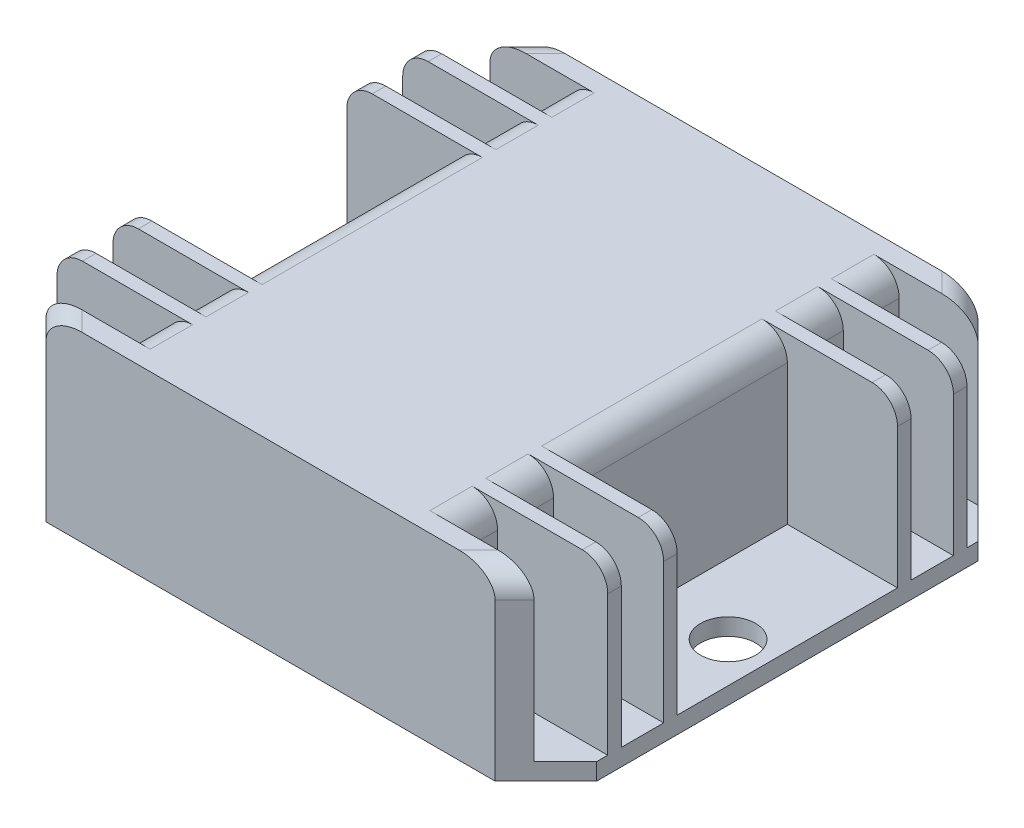
SolidWorks part; units mm, degrees
material "201.0-T43 Insulated Mold Casting (SS)"
ref_plane "Front Plane" through (0, 0, 0) normal (0, 0, 1) x (1, 0, 0)
ref_plane "Top Plane" through (0, 0, 0) normal (0, 1, 0) x (1, 0, 0)
ref_plane "Right Plane" through (0, 0, 0) normal (1, 0, 0) x (0, 0, -1)
sketch "Sketch1" plane through (0, 0, 0) normal (0, 1, 0) x (1, 0, 0)
  line L0 (0, -1000) -> (0, 49000) construction
  line L1 (-32.5, -28.5) -> (32.5, -28.5)
  line L2 (-32.5, -28.5) -> (-32.5, 28.5)
  line L3 (-32.5, 28.5) -> (32.5, 28.5)
  line L4 (32.5, -28.5) -> (32.5, 28.5)
  line L5 (-32.5, -28.5) -> (32.5, 28.5) construction
  line L6 (-32.5, 28.5) -> (32.5, -28.5) construction
  circle A0 centre (27.75, -2.25) radius 3.25
  circle A1 centre (-27.75, -2.25) radius 3.25
  point P0 (0, 0)
  dimension "D5" = 6.5
  dimension "D1" = 65
  dimension "D2" = 57
  dimension "D3" = 26.25
  dimension "D4" = 4.75
extrude "Boss-Extrude1" add sketch "Sketch1" along normal blind 21.5
chamfer "Chamfer1" distance 6 angle 45 4 edges at (32.5, 10.75, -28.5) (32.5, 10.75, 28.5) (-32.5, 10.75, -28.5) (-32.5, 10.75, 28.5)
sketch "Sketch2" plane through (0, 21.5, 0) normal (0, 1, 0) x (1, 0, 0)
  line L0 (-32.5, 22.5) -> (-32.5, -22.5) construction
  line L1 (-32.5, 13) -> (-19.5, 13)
  line L2 (-32.5, 13) -> (-32.5, -13)
  line L3 (-32.5, -13) -> (-19.5, -13)
  line L4 (-19.5, 13) -> (-19.5, -13)
  line L5 (0, -1000) -> (0, 49000) construction
  line L7 (-1000, 0) -> (49000, 0) construction
  line L8 (-32.5, 14.6) -> (-19.5, 14.6)
  line L9 (-32.5, 14.6) -> (-32.5, 19.6)
  line L10 (-32.5, 19.6) -> (-19.5, 19.6)
  line L11 (-19.5, 14.6) -> (-19.5, 19.6)
  line L12 (-32.5, 21.2) -> (-19.5, 21.2)
  line L13 (-32.5, 21.2) -> (-32.5, 26.2)
  line L14 (-32.5, 26.2) -> (-19.5, 26.2)
  line L15 (-19.5, 21.2) -> (-19.5, 26.2)
  line L16 (-32.5, -19.6) -> (-19.5, -19.6)
  line L17 (-19.5, -14.6) -> (-19.5, -19.6)
  line L18 (-32.5, -14.6) -> (-19.5, -14.6)
  line L19 (-32.5, -14.6) -> (-32.5, -19.6)
  line L20 (-32.5, -26.2) -> (-19.5, -26.2)
  line L21 (-19.5, -21.2) -> (-19.5, -26.2)
  line L22 (-32.5, -21.2) -> (-19.5, -21.2)
  line L23 (-32.5, -21.2) -> (-32.5, -26.2)
  line L24 (32.5, -21.2) -> (32.5, -26.2)
  line L25 (32.5, -21.2) -> (19.5, -21.2)
  line L26 (19.5, -21.2) -> (19.5, -26.2)
  line L27 (32.5, -26.2) -> (19.5, -26.2)
  line L28 (32.5, -14.6) -> (32.5, -19.6)
  line L29 (32.5, -14.6) -> (19.5, -14.6)
  line L30 (19.5, -14.6) -> (19.5, -19.6)
  line L31 (32.5, -19.6) -> (19.5, -19.6)
  line L32 (32.5, -13) -> (19.5, -13)
  line L33 (19.5, 13) -> (19.5, -13)
  line L34 (32.5, 13) -> (19.5, 13)
  line L35 (32.5, 13) -> (32.5, -13)
  line L36 (32.5, 19.6) -> (19.5, 19.6)
  line L37 (19.5, 14.6) -> (19.5, 19.6)
  line L38 (32.5, 14.6) -> (19.5, 14.6)
  line L39 (32.5, 14.6) -> (32.5, 19.6)
  line L40 (32.5, 26.2) -> (19.5, 26.2)
  line L41 (19.5, 21.2) -> (19.5, 26.2)
  line L42 (32.5, 21.2) -> (19.5, 21.2)
  line L43 (32.5, 21.2) -> (32.5, 26.2)
  point P6 (-32.5, 0)
  dimension "D1" = 26
  dimension "D2" = 13
  dimension "D3" = 5
  dimension "D4" = 5
  dimension "D5" = 1.6
  dimension "D6" = 1.6
extrude "Cut-Extrude1" cut sketch "Sketch2" against normal blind 19.5
fillet "Fillet1" radius 3 22 edges at (-19.5, 21.5, 23.7) (-19.5, 21.5, 17.1) (-19.5, 21.5, -23.7) (-19.5, 21.5, -17.1) (-19.5, 21.5, 0) (19.5, 21.5, 23.7) (19.5, 21.5, 17.1) (19.5, 21.5, 0) (19.5, 21.5, -17.1) (19.5, 21.5, -23.7) (27.65, 21.5, -27.35) (32.5, 21.5, -20.4) (32.5, 21.5, -13.8) (32.5, 21.5, 13.8) (32.5, 21.5, 20.4) (27.65, 21.5, 27.35) (-27.65, 21.5, -27.35) (-27.65, 21.5, 27.35) (-32.5, 21.5, 20.4) (-32.5, 21.5, 13.8) (-32.5, 21.5, -13.8) (-32.5, 21.5, -20.4)
